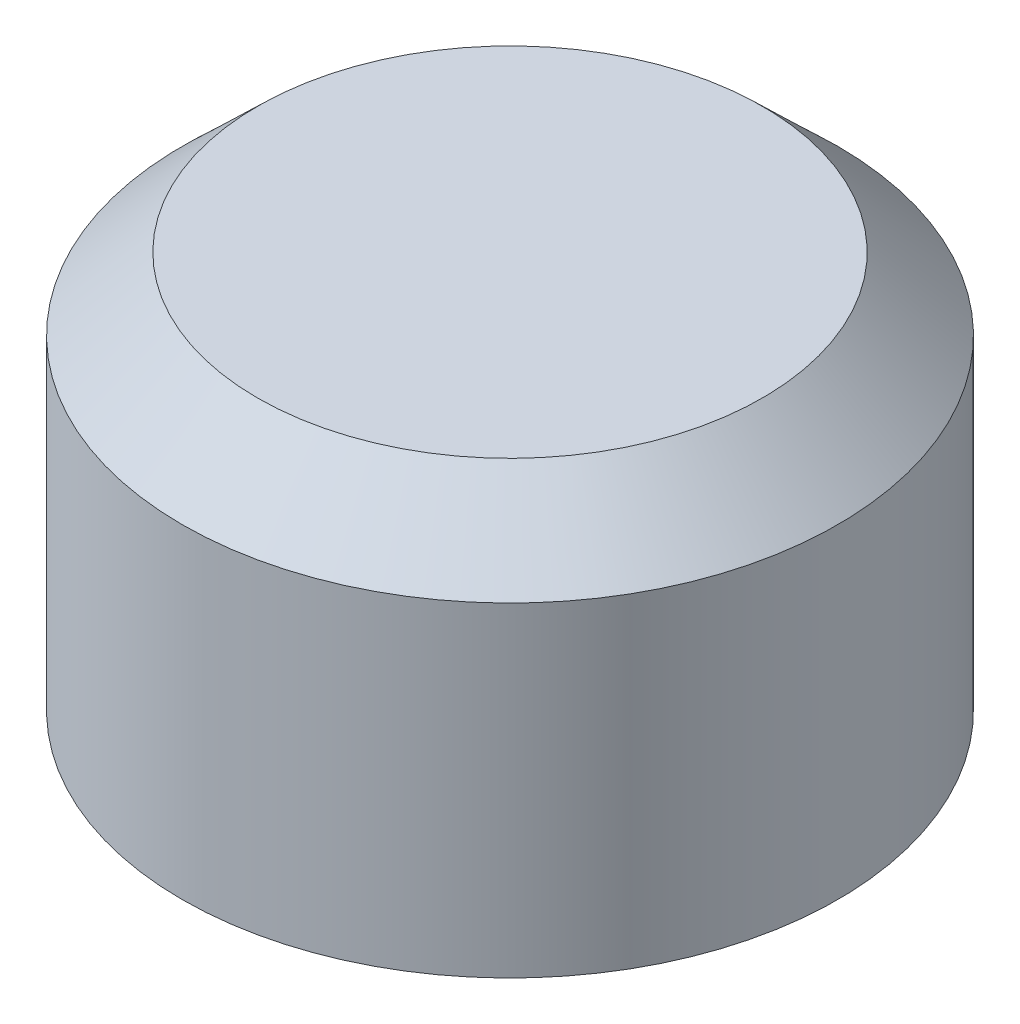
SolidWorks part; units mm, degrees
ref_plane "Front Plane" through (0, 0, 0) normal (0, 0, 1) x (1, 0, 0)
ref_plane "Top Plane" through (0, 0, 0) normal (0, 1, 0) x (1, 0, 0)
ref_plane "Right Plane" through (0, 0, 0) normal (1, 0, 0) x (0, 0, -1)
sketch "Sketch1" plane through (0, 0, 0) normal (0, 0, 1) x (1, 0, 0)
  line L0 (-2438.4, 0) -> (-2438.4, 2753.721)
  line L1 (-2438.4, 2753.721) -> (-2118.721, 3073.4)
  line L2 (-2118.721, 3073.4) -> (-1190.8772, 3073.4)
  line L3 (-1190.8772, 3073.4) -> (-914.4, 2796.9228)
  line L4 (-914.4, 2796.9228) -> (-914.4, 2074)
  line L6 (-939.8, 2074) -> (-939.8, 2786.4018)
  line L7 (-939.8, 2786.4018) -> (-1201.3982, 3048)
  line L8 (-1201.3982, 3048) -> (-2108.2, 3048)
  line L9 (-2108.2, 3048) -> (-2413, 2743.2)
  line L10 (-2413, 2743.2) -> (-2413, 0)
  line L11 (-2413, 0) -> (-2438.4, 0)
  line L12 (-914.4, 2074) -> (-364.1404, 1523.7404)
  line L13 (-364.1404, 1523.7404) -> (-389.5404, 1523.7404)
  line L14 (-389.5404, 1523.7404) -> (-939.8, 2074)
  point P2 (-939.8, 2074)
  point P14 (-914.4, 2074)
  dimension "D1" = 25.4
  dimension "D3" = 2743.2
  dimension "D4" = 304.8
  dimension "D5" = 304.8
  dimension "D6" = 25.4
  dimension "D8" = 25.4
  dimension "D9" = 25.4
  dimension "D11" = 2438.4
  dimension "D13" = 45
  dimension "D14" = 25.4
sketch "Sketch2" plane through (0, 0, 0) normal (0, 0, 1) x (1, 0, 0)
  line L0 (-2743.2, 0) -> (-2768.6, 0)
  line L1 (-2768.6, 0) -> (-2768.6, 2743.2)
  line L2 (-2743.2, 0) -> (-2743.2, 2732.3741)
  line L3 (-2743.2, 2732.3741) -> (-2123.3813, 3327.4)
  line L4 (-2123.3813, 3327.4) -> (0, 3327.4)
  line L5 (0, 3327.4) -> (0, 3352.8)
  line L6 (0, 3352.8) -> (-2133.6, 3352.8)
  line L7 (-2133.6, 3352.8) -> (-2768.6, 2743.2)
  dimension "D1" = 2743.2
  dimension "D2" = 2133.6
  dimension "D3" = 25.4
  dimension "D4" = 25.4
  dimension "D5" = 304.8
  dimension "D6" = 609.6
  dimension "D7" = 25.4
ref_axis "Axis1" through (0, 3520.44, 0) along (0, -1, 0)
revolve "Revolve1" add sketch "Sketch1" angle 360 about axis through (0, 3520.44, 0) along (0, -1, 0)
revolve "Revolve2" add sketch "Sketch2" angle 360 about axis through (0, 3520.44, 0) along (0, -1, 0)
